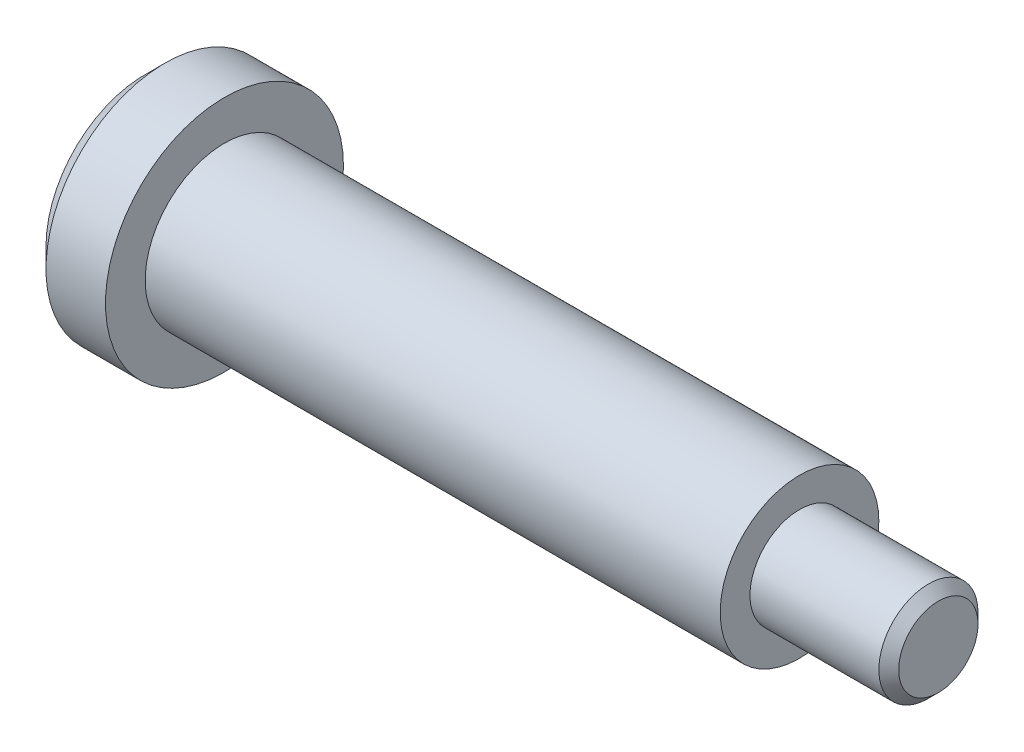
SolidWorks part; units mm, degrees
ref_plane "Front Plane" through (0, 0, 0) normal (0, 0, 1) x (1, 0, 0)
ref_plane "Top Plane" through (0, 0, 0) normal (0, 1, 0) x (1, 0, 0)
ref_plane "Right Plane" through (0, 0, 0) normal (1, 0, 0) x (0, 0, -1)
sketch "Sketch1" plane through (0, 0, 0) normal (1, 0, 0) x (0, 0, -1)
  circle A0 centre (0, 0) radius 6
  dimension "D1" = 12
extrude "Boss-Extrude1" add sketch "Sketch1" along normal blind 4
sketch "Sketch2" plane through (4, 0, 0) normal (1, 0, 0) x (0, 0, -1)
  circle A0 centre (0, 0) radius 4
  dimension "D1" = 8
extrude "Boss-Extrude2" add sketch "Sketch2" along normal blind 29
sketch "Sketch3" plane through (33, 0, 0) normal (1, 0, 0) x (0, 0, -1)
  circle A0 centre (0, 0) radius 2.5
  dimension "D1" = 5
extrude "Boss-Extrude3" add sketch "Sketch3" along normal blind 7
chamfer "Chamfer1" distance 0.5 angle 45 1 edges at (40, 0, -2.5)
chamfer "Chamfer2" distance 1 angle 45 1 edges at (0, 0, -6)
sketch "Sketch4" plane through (0, 0, 0) normal (-1, 0, 0) x (0, 0, 1)
  circle A0 centre (0, 0) radius 2.5
  dimension "D1" = 5
extrude "Cut-Extrude1" cut sketch "Sketch4" against normal blind 1
fillet "Fillet1" radius 0.5 1 edges at (0, 0, 2.5)
